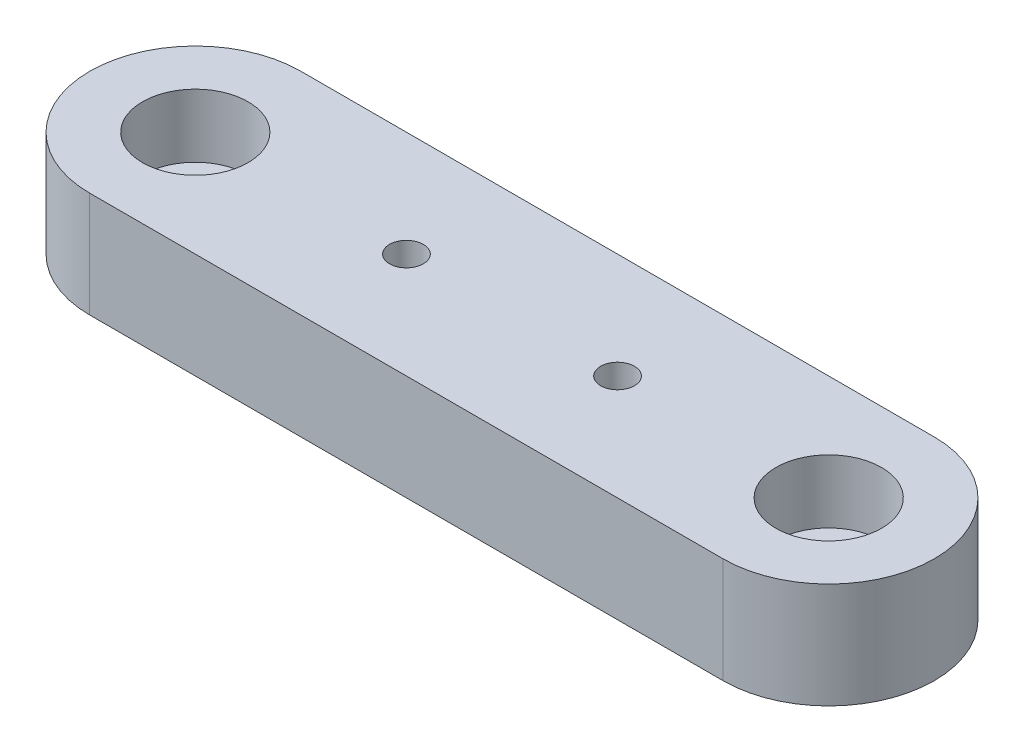
SolidWorks part; units mm, degrees
ref_plane "Front Plane" through (0, 0, 0) normal (0, 0, 1) x (1, 0, 0)
ref_plane "Top Plane" through (0, 0, 0) normal (0, 1, 0) x (1, 0, 0)
ref_plane "Right Plane" through (0, 0, 0) normal (1, 0, 0) x (0, 0, -1)
sketch "Sketch1" plane through (0, 0, 0) normal (0, 1, 0) x (1, 0, 0)
  line L0 (0, 10) -> (0, -10) construction
  line L1 (-40, 10) -> (40, 10)
  line L2 (-40, 10) -> (-40, -10)
  line L3 (-40, -10) -> (40, -10)
  line L4 (40, 10) -> (40, -10)
  line L5 (-40, 10) -> (40, -10) construction
  line L6 (-40, -10) -> (40, 10) construction
  line L7 (-40, 0) -> (40, 0) construction
  circle A0 centre (-10, 0) radius 1.6
  circle A2 centre (-30, 0) radius 3
  circle A3 centre (10, 0) radius 1.6
  circle A4 centre (30, 0) radius 3
  circle A5 centre (-30, 0) radius 10
  circle A6 centre (30, 0) radius 10
  point P0 (0, 0)
  dimension "D3" = 3.2
  dimension "D5" = 6
  dimension "D1" = 20
  dimension "D2" = 80
  dimension "D4" = 20
extrude "Boss-Extrude1" add sketch "Sketch1" along normal blind 10 contours A5 A2 | L3 A6 L1 A5 A0 A3 | A6 A4
sketch "Sketch2" plane through (0, 10, 0) normal (0, 1, 0) x (1, 0, 0)
  line L0 (0, 10) -> (0, -10) construction
  line L3 (-30, -10) -> (30, -10) construction
  line L4 (-30, 10) -> (30, 10) construction
  circle A0 centre (-30, 0) radius 5
  circle A1 centre (30, 0) radius 5
  dimension "D1" = 10
extrude "Cut-Extrude1" cut sketch "Sketch2" against normal blind 6
hole_wizard "CSK for M3 Flat Head Machine Screw1" positions "Sketch3" profile "Sketch4" countersink size "M3" standard "ANSI Metric" end condition up to next
sketch "Sketch3" plane through (0, 0, 0) normal (0, -1, 0) x (-1, 0, 0)
  point P0 (10, 0)
  point P3 (-10, 0)
sketch "Sketch4" plane through (-10, 0, 0) normal (1, 0, 0) x (0, 0, -1)
  line L0 (0, 0) -> (0, 10)
  line L1 (0, 10) -> (1.5, 10)
  line L2 (1.5, 10) -> (1.5, 1.8)
  line L3 (1.5, 1.8) -> (3, 0.3)
  line L4 (3, 0.3) -> (3, 0)
  line L6 (3, 0) -> (0, 0)
  line L7 (-1.5, 1.8) -> (-3, 0.3) construction
  line L11 (0, -6.35) -> (0, 107.95) construction
  dimension "Thru Hole Dia." = 3
  dimension "Thru Hole Depth" = 10
  dimension "C'Sink Dia." = 6
  dimension "C'Sink Angle" = 90
  dimension "Head Clearance" = 0.3
